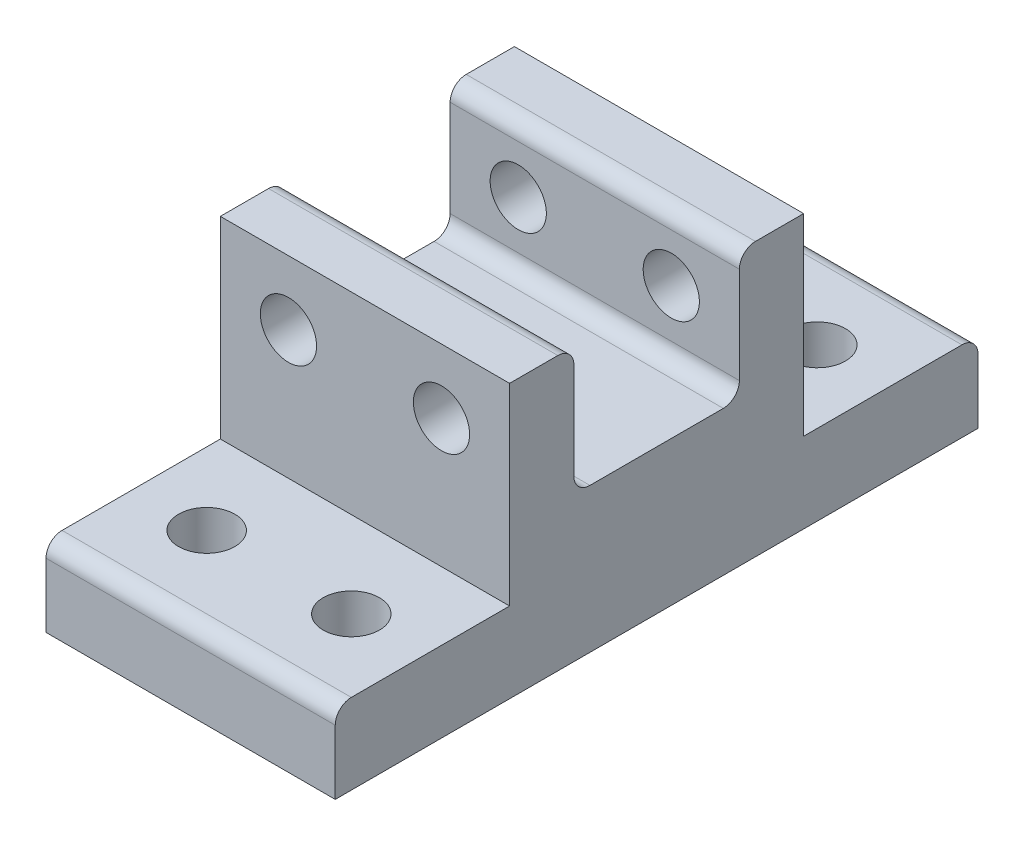
SolidWorks part; units mm, degrees
ref_plane "Front Plane" through (0, 0, 0) normal (0, 0, 1) x (1, 0, 0)
ref_plane "Top Plane" through (0, 0, 0) normal (0, 1, 0) x (1, 0, 0)
ref_plane "Right Plane" through (0, 0, 0) normal (1, 0, 0) x (0, 0, -1)
sketch "Sketch1" plane through (0, 0, 0) normal (0, 1, 0) x (1, 0, 0)
  line L1 (-9, -9.15) -> (9, -9.15)
  line L2 (-9, -9.15) -> (-9, 9.15)
  line L3 (-9, 9.15) -> (9, 9.15)
  line L4 (9, -9.15) -> (9, 9.15)
  line L5 (-9, -9.15) -> (9, 9.15) construction
  line L6 (-9, 9.15) -> (9, -9.15) construction
  point P0 (0, 0)
  dimension "D1" = 18
  dimension "D2" = 18.3
extrude "Boss-Extrude1" add sketch "Sketch1" along normal blind 3 contours L2 L1 L4 L3
sketch "Sketch2" plane through (0, 3, 0) normal (0, 1, 0) x (1, 0, 0)
  line L0 (-9, -9.15) -> (-9, 9.15) construction
  line L1 (9, -9.15) -> (-9, -9.15)
  line L2 (9, -9.15) -> (9, -5.15)
  line L3 (9, -5.15) -> (-9, -5.15)
  line L4 (-9, -9.15) -> (-9, -5.15)
  line L6 (9, 9.15) -> (-9, 9.15)
  line L7 (9, 9.15) -> (9, 5.15)
  line L8 (9, 5.15) -> (-9, 5.15)
  line L9 (-9, 9.15) -> (-9, 5.15)
  dimension "D1" = 4
extrude "Boss-Extrude3" add sketch "Sketch2" along normal blind 8
sketch "Sketch3" plane through (0, 0, 5.15) normal (0, 0, -1) x (-1, 0, 0)
  line L0 (-9, 11) -> (-4.762, 11) construction
  line L1 (-9, 11) -> (9, 11) construction
  line L2 (-4.762, 11) -> (-4.762, 3) construction
  line L3 (-9, 3) -> (9, 3) construction
  line L4 (0, 11) -> (0, 3) construction
  circle A0 centre (-4.762, 7) radius 1.75
  circle A1 centre (4.762, 7) radius 1.75
  dimension "D2" = 3.5
  dimension "D1" = 4.238
extrude "Cut-Extrude2" cut sketch "Sketch3" against normal blind 13 and the other way blind 20
fillet "Fillet1" radius 1 1 edges at (0, 3, 5.15)
fillet "Fillet2" radius 1 1 edges at (0, 3, -5.15)
fillet "Fillet3" radius 1 2 edges at (0, 11, -5.15) (0, 11, 5.15)
sketch "Sketch4" plane through (0, 0, 0) normal (0, -1, 0) x (1, 0, 0)
  line L1 (-9, 9.15) -> (9, 9.15)
  line L2 (-9, 9.15) -> (-9, -9.15)
  line L3 (-9, -9.15) -> (9, -9.15)
  line L4 (9, 9.15) -> (9, -9.15)
  line L5 (-9, 9.15) -> (9, -9.15) construction
  line L6 (-9, -9.15) -> (9, 9.15) construction
  point P0 (0, 0)
extrude "Boss-Extrude4" add sketch "Sketch4" along normal blind 1
sketch "Sketch5" plane through (0, -1, 0) normal (0, -1, 0) x (-1, 0, 0)
  line L1 (9, -20) -> (-9, -20)
  line L2 (9, -20) -> (9, 20)
  line L3 (9, 20) -> (-9, 20)
  line L4 (-9, -20) -> (-9, 20)
  line L5 (9, -20) -> (-9, 20) construction
  line L6 (9, 20) -> (-9, -20) construction
  point P0 (0, 0)
  dimension "D1" = 40
extrude "Boss-Extrude5" add sketch "Sketch5" along normal blind 5
sketch "Sketch6" plane through (0, -6, 0) normal (0, -1, 0) x (1, 0, 0)
  line L0 (0, 20) -> (0, -20) construction
  line L1 (9, 20) -> (-9, 20) construction
  line L2 (-9, -20) -> (9, -20) construction
  line L3 (9, 0) -> (-9, 0) construction
  line L4 (9, -20) -> (9, 20) construction
  line L5 (-9, 20) -> (-9, -20) construction
  line L6 (9, 20) -> (9, 14.5) construction
  line L8 (9, 14.5) -> (0, 14.5) construction
  circle A0 centre (4.5, 14.5) radius 1.75
  circle A1 centre (-4.5, 14.5) radius 1.75
  circle A2 centre (-4.5, -14.5) radius 1.75
  circle A3 centre (4.5, -14.5) radius 1.75
  dimension "D2" = 3.5
  dimension "D1" = 5.5
extrude "Cut-Extrude4" cut sketch "Sketch6" against normal blind 5
fillet "Fillet4" radius 1 1 edges at (0, -1, -20)
fillet "Fillet5" radius 1 1 edges at (0, -1, 20)
